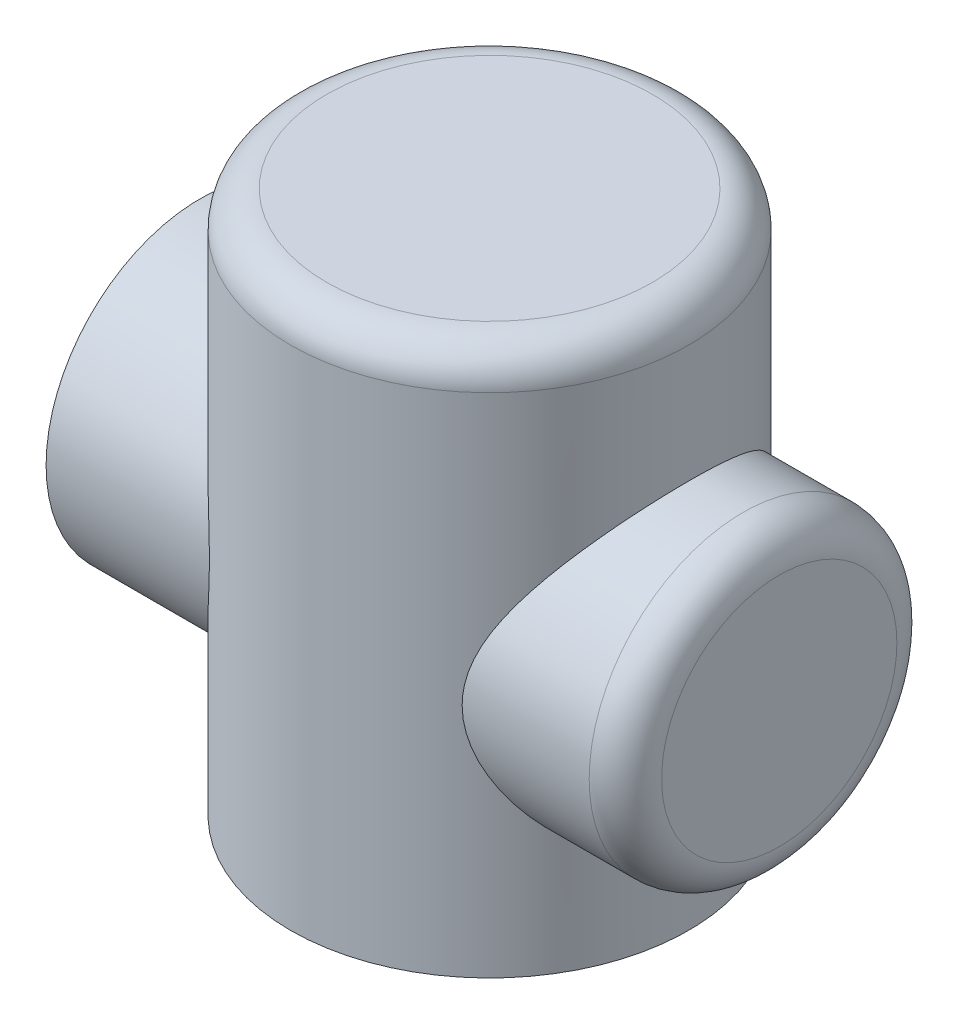
SolidWorks part; units mm, degrees
ref_plane "Front Plane" through (0, 0, 0) normal (0, 0, 1) x (1, 0, 0)
ref_plane "Top Plane" through (0, 0, 0) normal (0, 1, 0) x (1, 0, 0)
ref_plane "Right Plane" through (0, 0, 0) normal (1, 0, 0) x (0, 0, -1)
sketch "Sketch1" plane through (0, 0, 0) normal (0, 1, 0) x (1, 0, 0)
  circle A0 centre (0, 0) radius 55
  dimension "D1" = 110
extrude "Boss-Extrude1" add sketch "Sketch1" along normal blind 150
sketch "Sketch3" plane through (0, 0, 0) normal (1, 0, 0) x (0, 0, -1)
  circle A0 centre (0, 65) radius 42.5
  dimension "D1" = 85
sketch "Sketch11" plane through (0, 0, 0) normal (0, 1, 0) x (1, 0, 0)
  circle A0 centre (0, 0) radius 42.5
  dimension "D1" = 85
extrude "Cut-Extrude9" cut sketch "Sketch11" along normal blind 65 and the other way blind 1 contours A0
fillet "Fillet5" radius 10 1 edges at (0, 150, 55)
extrude "Boss-Extrude6" add sketch "Sketch3" along normal mid plane 160 contours A0
fillet "Fillet7" radius 10 1 edges at (80, 65, -42.5)
